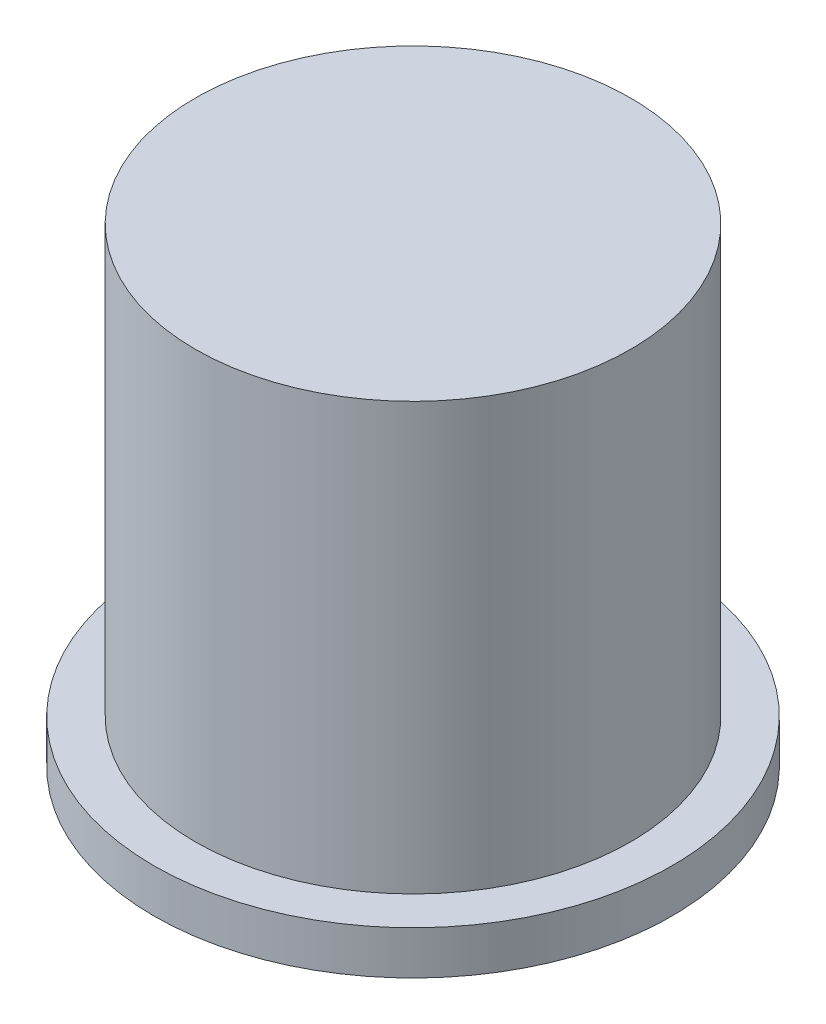
SolidWorks part; units mm, degrees
ref_plane "Front Plane" through (0, 0, 0) normal (0, 0, 1) x (1, 0, 0)
ref_plane "Top Plane" through (0, 0, 0) normal (0, 1, 0) x (1, 0, 0)
ref_plane "Right Plane" through (0, 0, 0) normal (1, 0, 0) x (0, 0, -1)
sketch "Sketch1" plane through (0, 0, 0) normal (0, 1, 0) x (1, 0, 0)
  circle A0 centre (0, 0) radius 6.35
  circle A2 centre (0, 0) radius 4.699
  dimension "D1" = 12.7
  dimension "D2" = 9.398
extrude "Boss-Extrude1" add sketch "Sketch1" along normal blind 13.716
sketch "Sketch2" plane through (0, 0, 0) normal (0, 1, 0) x (1, 0, 0)
  circle A0 centre (0, 0) radius 7.5565
  circle A1 centre (0, 0) radius 6.096
  dimension "D1" = 15.113
extrude "Boss-Extrude2" add sketch "Sketch2" along normal blind 1.27
sketch "Sketch3" plane through (0, 13.716, 0) normal (0, 1, 0) x (1, 0, 0)
  circle A0 centre (0, 0) radius 6.35
extrude "Boss-Extrude3" add sketch "Sketch3" against normal blind 1.016
